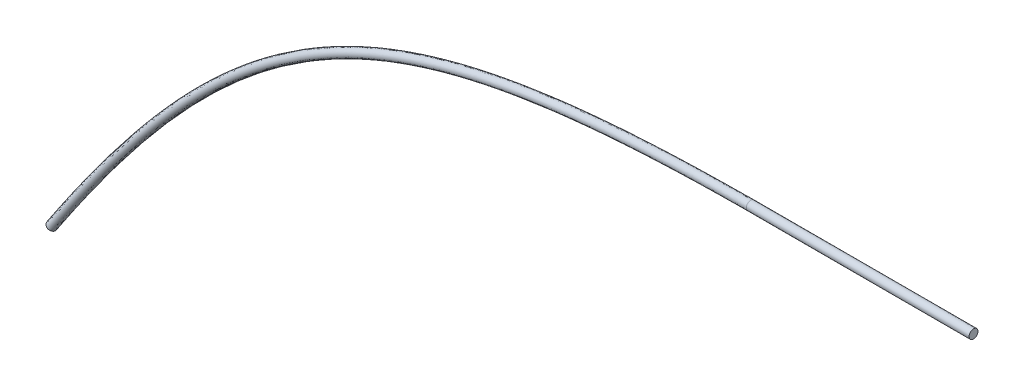
SolidWorks part; units mm, degrees
ref_plane "Front Plane" through (0, 0, 0) normal (0, 0, 1) x (1, 0, 0)
ref_plane "Top Plane" through (0, 0, 0) normal (0, 1, 0) x (1, 0, 0)
ref_plane "Right Plane" through (0, 0, 0) normal (1, 0, 0) x (0, 0, -1)
sketch "Sketch1" plane through (8.3788, 0.0004, 0) normal (-1, 0, 0) x (0, 0, 1)
  line L0 (6.1691, 35.1585) -> (6.1691, 26.5225) construction
  line L4 (1.8511, 35.1585) -> (1.8511, 26.5225)
  line L5 (1.8511, 26.5225) -> (10.4871, 26.5225)
  line L6 (10.4871, 26.5225) -> (10.4871, 35.1585)
  line L7 (10.4871, 35.1585) -> (1.8511, 35.1585)
  line L8 (1.8511, 35.1585) -> (1.8511, 26.5225)
  line L9 (1.8511, 26.5225) -> (10.4871, 26.5225)
  line L10 (10.4871, 26.5225) -> (10.4871, 35.1585)
  line L11 (10.4871, 35.1585) -> (1.8511, 35.1585)
  circle A0 centre (6.1691, 30.8405) radius 0.254
  dimension "D1" = 0
sketch "Sketch2" plane through (-20.479, 20.479, 0) normal (-0.7071, 0.7071, 0) x (0, 0, 1)
  line L4 (-18.5129, -13.9515) -> (-18.5129, -43.7965)
  line L5 (-18.5129, -43.7965) -> (39.4871, -43.7965)
  line L6 (39.4871, -43.7965) -> (39.4871, -13.9515)
  line L7 (39.4871, -13.9515) -> (-18.5129, -13.9515)
  line L8 (-18.5129, -13.9515) -> (-18.5129, -43.7965)
  line L9 (-18.5129, -43.7965) -> (39.4871, -43.7965)
  line L10 (39.4871, -43.7965) -> (39.4871, -13.9515)
  line L11 (39.4871, -13.9515) -> (-18.5129, -13.9515)
  dimension "D1" = 0
extrude "Extrude1" add sketch "Sketch1" against normal blind 12.7 contours A0 L0 | L0 A0
sketch "Sketch3" plane through (8.3788, 0.0004, 0) normal (-1, 0, 0) x (0, 0, 1)
  line L0 (6.1691, 30.8405) -> (6.1691, 31.0945) construction
  circle A0 centre (6.1691, 30.8405) radius 0.254
ref_plane "Plane1" through (0, 0, 6.1691) normal (0, 0, 1) x (1, 0, 0)
sketch "Sketch4" plane through (0, 0, 6.1691) normal (0, 0, 1) x (1, 0, 0)
  spline S0 degree 3 poles (8.3773, 30.8409) (-12.0316, 30.7141) (-20.1484, 26.9375) (-31.4691, 9.9132) knots 0 0 0 0 1 1 1 1
sweep "Sweep1" add profiles "Sketch3" path "Sketch4"
